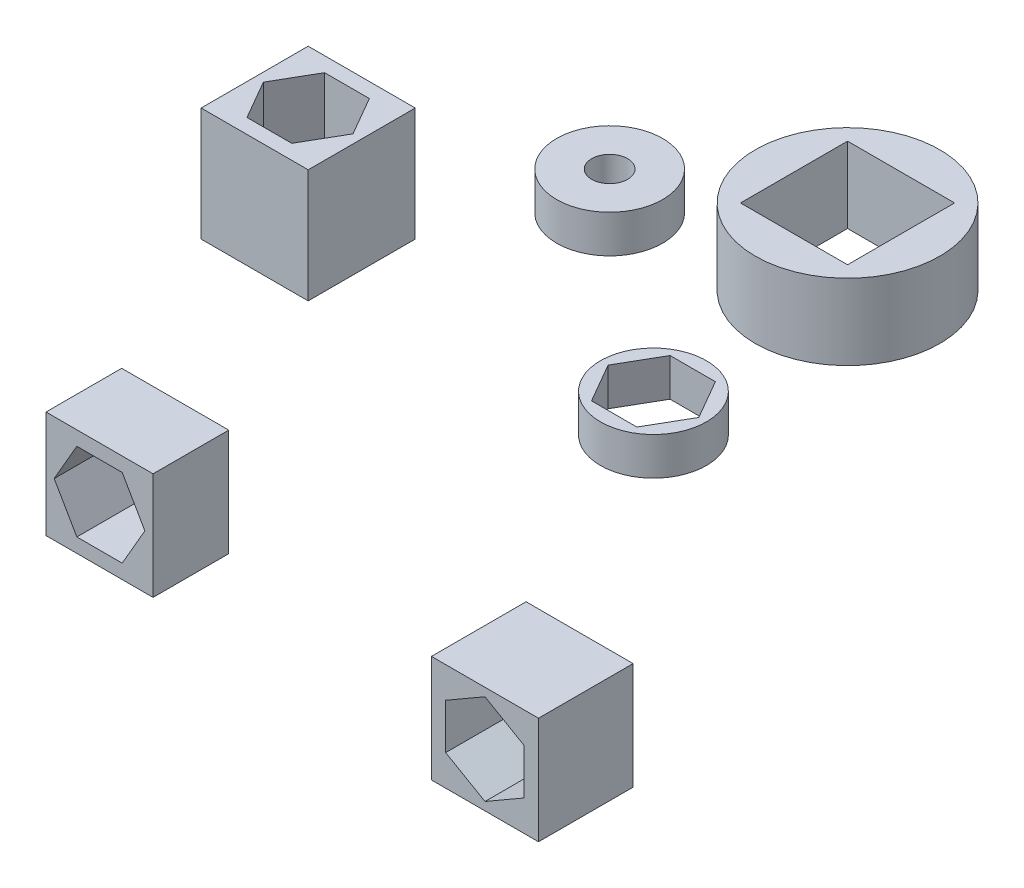
SolidWorks part; units mm, degrees
ref_plane "前视基准面" through (0, 0, 0) normal (0, 0, 1) x (1, 0, 0)
ref_plane "上视基准面" through (0, 0, 0) normal (0, 1, 0) x (1, 0, 0)
ref_plane "右视基准面" through (0, 0, 0) normal (1, 0, 0) x (0, 0, -1)
sketch "草图1" plane through (0, 0, 0) normal (0, 1, 0) x (1, 0, 0)
  line L1 (-32.3643, 16.6549) -> (-33.5623, 18.7299)
  line L2 (-50.0178, 19.3243) -> (-55.6746, 19.3243)
  line L3 (-50.0178, 19.3243) -> (-50.0178, 13.6675)
  line L4 (-50.0178, 13.6675) -> (-55.6746, 13.6675)
  line L5 (-55.6746, 19.3243) -> (-55.6746, 13.6675)
  line L6 (-33.5623, 18.7299) -> (-35.9583, 18.7299)
  line L7 (-35.9583, 18.7299) -> (-37.1563, 16.6549)
  line L8 (-37.1563, 16.6549) -> (-35.9583, 14.5799)
  line L9 (-35.9583, 14.5799) -> (-33.5623, 14.5799)
  line L10 (-33.5623, 14.5799) -> (-32.3643, 16.6549)
  line L11 (-50.4791, 16.4959) -> (-51.6626, 18.5459)
  line L12 (-51.6626, 18.5459) -> (-54.0298, 18.5459)
  line L13 (-54.0298, 18.5459) -> (-55.2134, 16.4959)
  line L14 (-55.2134, 16.4959) -> (-54.0298, 14.4459)
  line L15 (-54.0298, 14.4459) -> (-51.6626, 14.4459)
  line L16 (-51.6626, 14.4459) -> (-50.4791, 16.4959)
  circle A0 centre (-34.7603, 16.6549) radius 2.8
  circle A1 centre (-34.7603, 16.6549) radius 2.075 construction
  circle A2 centre (-46.0895, 25.6699) radius 2.8
  circle A3 centre (-46.0895, 25.6699) radius 0.95
  circle A4 centre (-52.8462, 16.4959) radius 2.05 construction
  dimension "D2" = 5.6
  dimension "D4" = 5.6
  dimension "D5" = 1.9
  dimension "D6" = 4.1
  dimension "D1" = 8
  dimension "D3" = 4.15
extrude "凸台-拉伸1" add sketch "草图1" along normal blind 6
sketch "草图2" plane through (0, 6, 0) normal (0, 1, 0) x (1, 0, 0)
  circle A0 centre (-46.0895, 25.6699) radius 2.8
extrude "切除-拉伸1" cut sketch "草图2" against normal blind 4
sketch "草图3" plane through (0, 6, 0) normal (0, 1, 0) x (1, 0, 0)
  circle A0 centre (-34.7603, 16.6549) radius 2.8
extrude "切除-拉伸2" cut sketch "草图3" against normal blind 4
sketch "草图4" plane through (0, 0, 0) normal (0, 1, 0) x (1, 0, 0)
  line L3 (-33.4216, 31.2296) -> (-39.0785, 31.2296)
  line L4 (-33.4216, 31.2296) -> (-33.4216, 25.5728)
  line L5 (-33.4216, 25.5728) -> (-39.0785, 25.5728)
  line L6 (-39.0785, 31.2296) -> (-39.0785, 25.5728)
  circle A0 centre (-36.2501, 28.4012) radius 4.875
  dimension "D1" = 9.75
  dimension "D2" = 4
  dimension "D3" = 4
extrude "凸台-拉伸2" add sketch "草图4" along normal blind 4 separate body
sketch "草图6" plane through (0, 0, 0) normal (0, 1, 0) x (1, 0, 0)
  line L3 (-40.5478, 20.3536) -> (-46.2046, 20.3536)
  line L4 (-40.5478, 20.3536) -> (-40.5478, 14.6967)
  line L5 (-40.5478, 14.6967) -> (-46.2046, 14.6967)
  line L6 (-46.2046, 20.3536) -> (-46.2046, 14.6967)
sketch "草图7" plane through (0, 0, 0) normal (0, 0, 1) x (1, 0, 0)
  line L1 (-40.5478, 0) -> (-46.2046, 0) construction
  line L4 (-40.5478, 5.6569) -> (-46.2046, 5.6569)
  line L5 (-40.5478, 5.6569) -> (-40.5478, 0)
  line L6 (-40.5478, 0) -> (-46.2046, 0)
  line L7 (-46.2046, 5.6569) -> (-46.2046, 0)
extrude "凸台-拉伸3" add sketch "草图7" along normal blind 4 separate body
sketch "草图8" plane through (0, 0, 4) normal (0, 0, 1) x (1, 0, 0)
  line L1 (-40.9802, 2.8284) -> (-42.1782, 4.9034)
  line L2 (-42.1782, 4.9034) -> (-44.5742, 4.9034)
  line L3 (-44.5742, 4.9034) -> (-45.7722, 2.8284)
  line L4 (-45.7722, 2.8284) -> (-44.5742, 0.7534)
  line L5 (-44.5742, 0.7534) -> (-42.1782, 0.7534)
  line L6 (-42.1782, 0.7534) -> (-40.9802, 2.8284)
  circle A0 centre (-43.3762, 2.8284) radius 2.075 construction
  dimension "D1" = 4.15
extrude "切除-拉伸3" cut sketch "草图8" against normal blind 4
extrude "凸台-拉伸4" add sketch "草图6" along normal blind 4 separate body
sketch "草图9" plane through (0, 4, 0) normal (0, 1, 0) x (1, 0, 0)
  circle A0 centre (-43.4507, 17.5114) radius 4.7573
extrude "切除-拉伸4" cut sketch "草图9" against normal blind 4
sketch "草图15" plane through (0, 0, 0) normal (0, 1, 0) x (1, 0, 0)
  line L0 (-24.8363, 18.7261) -> (-15.024, 18.7261)
  line L1 (-24.8363, 18.7261) -> (-24.8363, 9.5984)
  line L2 (-15.024, 18.7261) -> (-15.024, 9.5984)
  line L3 (-24.8363, 9.5984) -> (-15.024, 9.5984)
sketch "草图16" plane through (0, 0, 0) normal (0, 0, 1) x (1, 0, 0)
  line L1 (-24.8363, 0) -> (-15.024, 0) construction
  line L2 (-24.8363, 0) -> (-15.024, 0) construction
  line L4 (-19.1794, 5.6569) -> (-24.8363, 5.6569)
  line L5 (-19.1794, 5.6569) -> (-19.1794, 0)
  line L6 (-19.1794, 0) -> (-24.8363, 0)
  line L7 (-24.8363, 5.6569) -> (-24.8363, 0)
  line L8 (-22.0078, 5.2244) -> (-24.0828, 4.0264)
  line L9 (-24.0828, 4.0264) -> (-24.0828, 1.6304)
  line L10 (-24.0828, 1.6304) -> (-22.0078, 0.4324)
  line L11 (-22.0078, 0.4324) -> (-19.9328, 1.6304)
  line L12 (-19.9328, 1.6304) -> (-19.9328, 4.0264)
  line L13 (-19.9328, 4.0264) -> (-22.0078, 5.2244)
  circle A0 centre (-22.0078, 2.8284) radius 2.075 construction
  dimension "D1" = 4.15
  dimension "D2" = 8
extrude "凸台-拉伸5" add sketch "草图15" along normal blind 4 separate body
sketch "草图17" plane through (0, 4, 0) normal (0, 1, 0) x (1, 0, 0)
  line L0 (-26.7618, 19.2952) -> (-26.7618, 9.4701)
  line L1 (-26.7618, 9.4701) -> (-13.0704, 9.4701)
  line L2 (-13.0704, 9.4701) -> (-13.4343, 20.7053)
  line L3 (-13.4343, 20.7053) -> (-26.7618, 19.2952)
extrude "切除-拉伸5" cut sketch "草图17" against normal blind 4
extrude "凸台-拉伸6" add sketch "草图16" along normal blind 5 separate body
